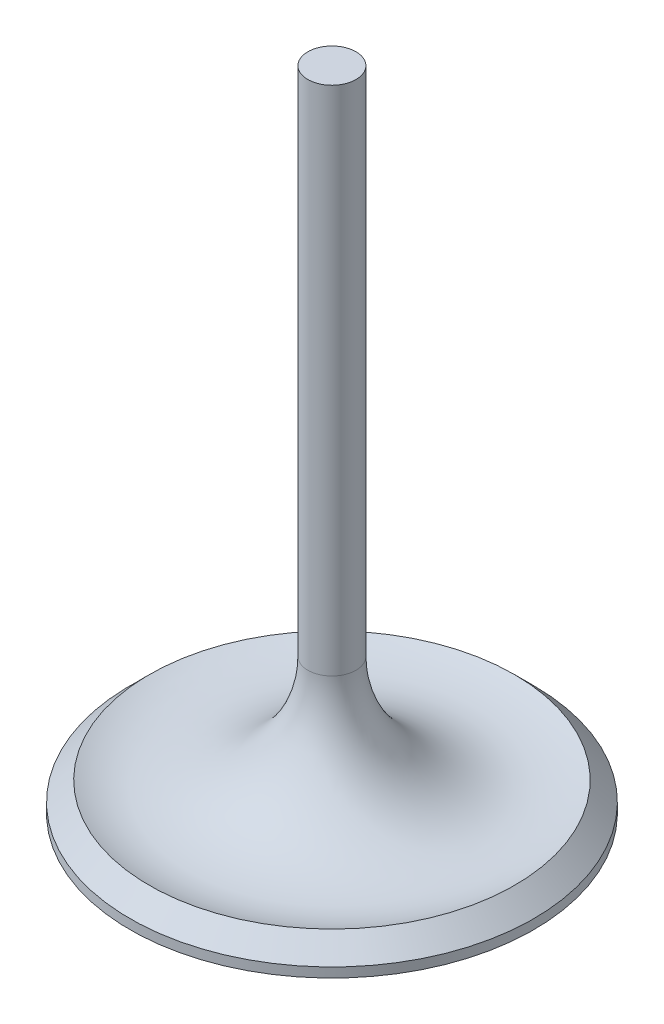
SolidWorks part; units mm, degrees
ref_plane "Front Plane" through (0, 0, 0) normal (0, 0, 1) x (1, 0, 0)
ref_plane "Top Plane" through (0, 0, 0) normal (0, 1, 0) x (1, 0, 0)
ref_plane "Right Plane" through (0, 0, 0) normal (1, 0, 0) x (0, 0, -1)
sketch "Sketch1" plane through (0, 0, 0) normal (0, 0, 1) x (1, 0, 0)
  line L0 (0, 0) -> (0, 85.55)
  line L1 (0, 85.55) -> (3.18, 85.55)
  line L2 (3.18, 85.55) -> (3.18, 17.9547)
  line L3 (24.13, 3.81) -> (26.67, 1.27)
  line L4 (26.67, 1.27) -> (26.67, 0)
  line L5 (0, 0) -> (26.67, 0)
  arc A0 (3.18, 17.9547) -> (24.13, 3.81) centre (18.43, 17.9547) ccw
  point P9 (0, 0)
  point P10 (0, 0)
  dimension "D7" = 15.25
  dimension "D1" = 85.55
  dimension "D2" = 26.67
  dimension "D3" = 3.18
  dimension "D4" = 1.27
  dimension "D5" = 3.81
  dimension "D6" = 45
revolve "Revolve1" add sketch "Sketch1" angle 360 about L0
